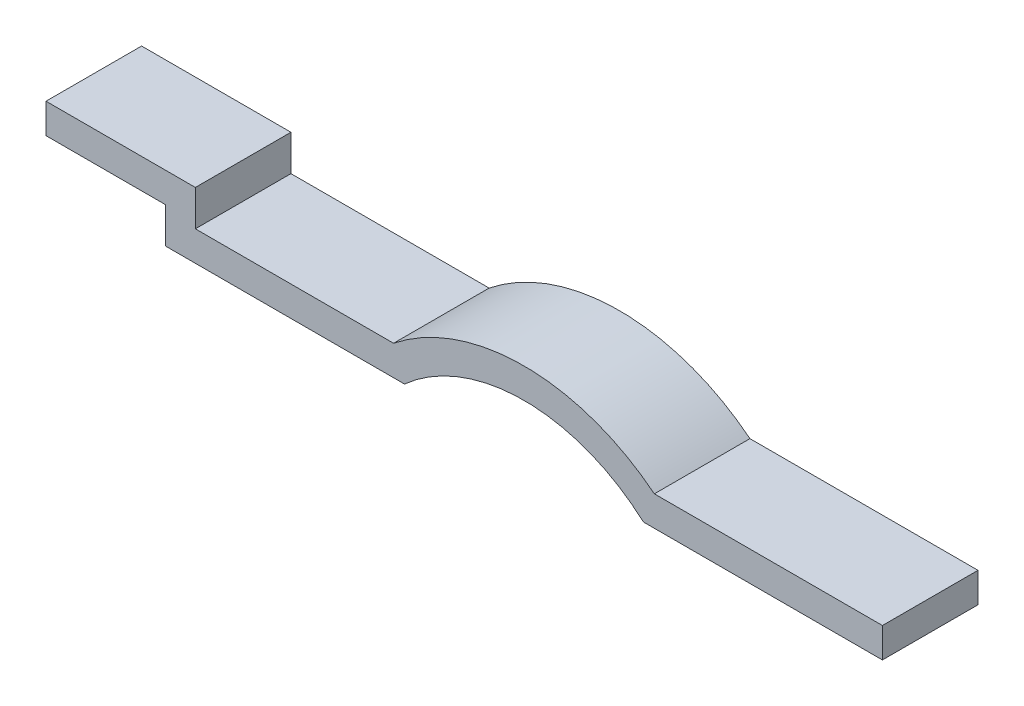
SolidWorks part; units mm, degrees
ref_plane "Front Plane" through (0, 0, 0) normal (0, 0, 1) x (1, 0, 0)
ref_plane "Top Plane" through (0, 0, 0) normal (0, 1, 0) x (1, 0, 0)
ref_plane "Right Plane" through (0, 0, 0) normal (1, 0, 0) x (0, 0, -1)
sketch "Sketch1" plane through (0, 0, 0) normal (0, 0, 1) x (1, 0, 0)
  line L0 (0, 0) -> (-200, 0)
  line L1 (-400, 0) -> (-600, 0)
  line L2 (-600, 0) -> (-600, 30)
  line L3 (-600, 30) -> (-700, 30)
  line L4 (0, 25) -> (-190.8678, 25)
  line L5 (-409.1322, 25) -> (-575, 25)
  line L6 (-575, 25) -> (-575, 55)
  line L7 (-575, 55) -> (-700, 55)
  line L8 (-700, 30) -> (-700, 55)
  line L9 (0, 25) -> (0, 0)
  arc A0 (-400, 0) -> (-200, 0) centre (-300, -111.8034) cw
  arc A1 (-409.1322, 25) -> (-190.8678, 25) centre (-300, -111.8034) cw
  dimension "D2" = 150
  dimension "D1" = 200
  dimension "D3" = 200
  dimension "D4" = 100
  dimension "D5" = 30
  dimension "D6" = 200
  dimension "D7" = 25
extrude "Boss-Extrude1" add sketch "Sketch1" along normal blind 80
